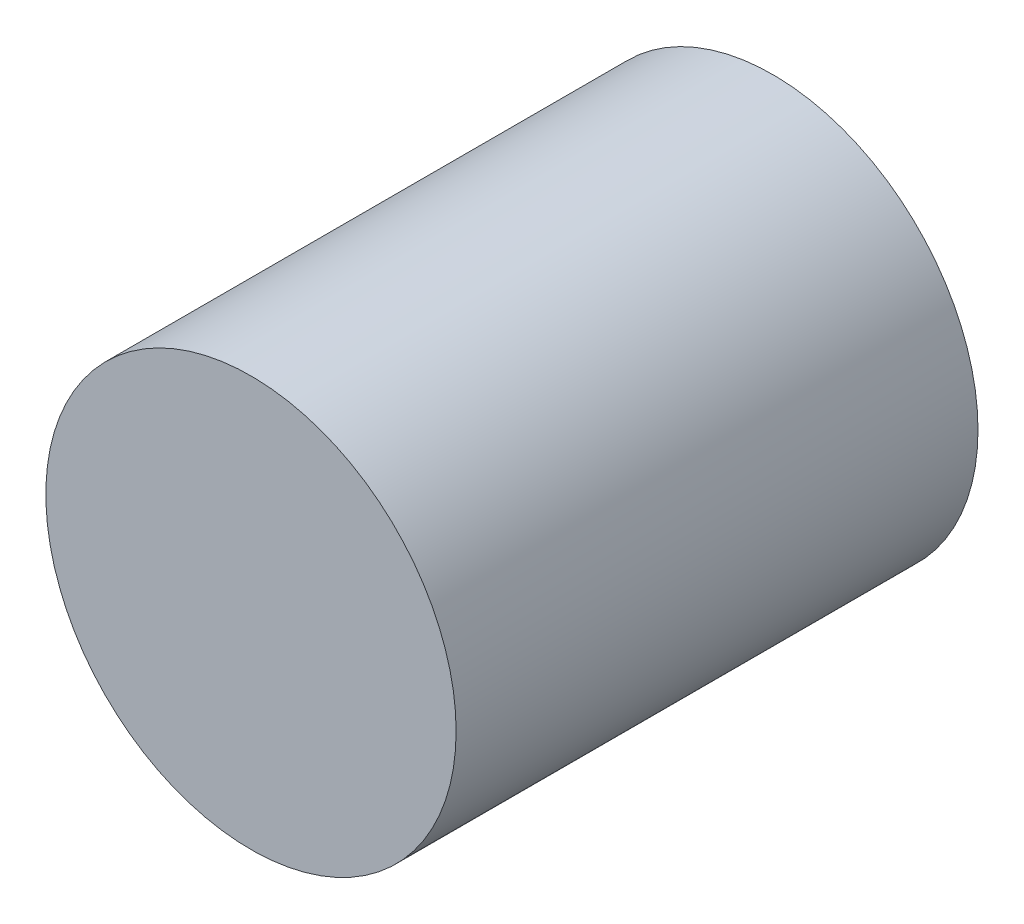
SolidWorks part; units mm, degrees
ref_plane "Front Plane" through (0, 0, 0) normal (0, 0, 1) x (1, 0, 0)
ref_plane "Top Plane" through (0, 0, 0) normal (0, 1, 0) x (1, 0, 0)
ref_plane "Right Plane" through (0, 0, 0) normal (1, 0, 0) x (0, 0, -1)
sketch "Sketch2" plane through (0, 0, 0) normal (0, 0, 1) x (1, 0, 0)
  circle A0 centre (0, 0) radius 11.95
  dimension "D1" = 23.9
extrude "Boss-Extrude1" add sketch "Sketch2" along normal blind 30.4
sketch "Sketch4" plane through (0, 0, 0) normal (0, 0, -1) x (-1, 0, 0)
  circle A1 centre (0, 8.95) radius 1.5
  circle A2 centre (0, -8.95) radius 1.5
  dimension "D2" = 3
  dimension "D4" = 3
extrude "Cut-Extrude2" cut sketch "Sketch4" against normal blind 3
sketch "Sketch5" plane through (0, 0, 0) normal (0, 0, -1) x (-1, 0, 0)
  circle A0 centre (0, 0) radius 0.99
  dimension "D1" = 1.98
extrude "Boss-Extrude2" add sketch "Sketch5" along normal blind 6.9
